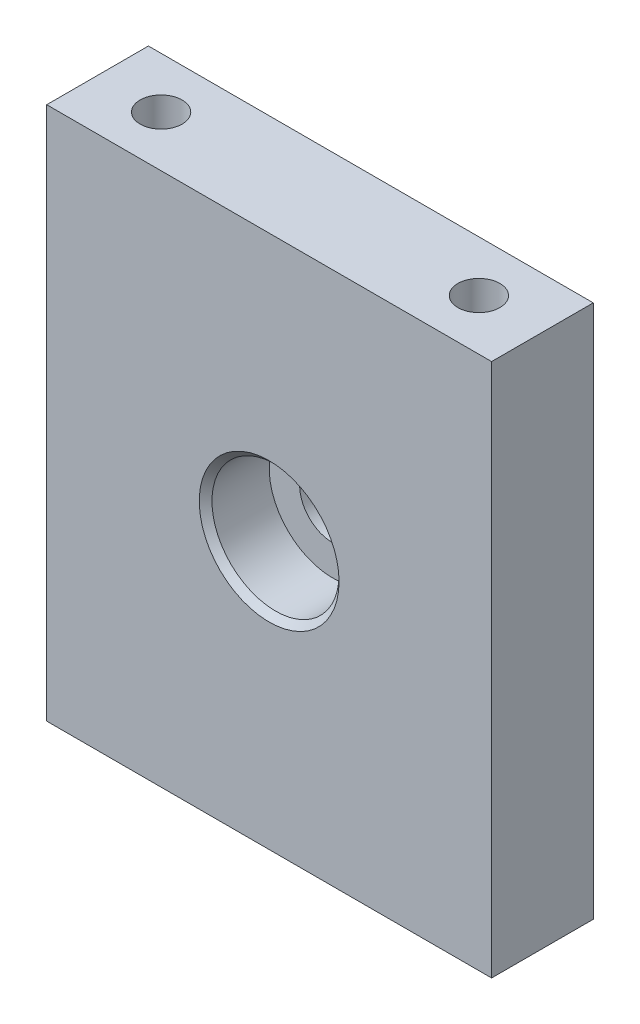
SolidWorks part; units mm, degrees
material "6061 合金"
ref_plane "前视基准面" through (0, 0, 0) normal (0, 0, 1) x (1, 0, 0)
ref_plane "上视基准面" through (0, 0, 0) normal (0, 1, 0) x (1, 0, 0)
ref_plane "右视基准面" through (0, 0, 0) normal (1, 0, 0) x (0, 0, -1)
sketch "草图1" plane through (0, 0, 0) normal (0, 0, 1) x (1, 0, 0)
  line L1 (-17.5, 21) -> (17.5, 21)
  line L2 (-17.5, 21) -> (-17.5, -21)
  line L3 (-17.5, -21) -> (17.5, -21)
  line L4 (17.5, 21) -> (17.5, -21)
  line L5 (-17.5, 21) -> (17.5, -21) construction
  line L6 (-17.5, -21) -> (17.5, 21) construction
  point P0 (0, 0)
  dimension "D1" = 42
  dimension "D2" = 35
extrude "凸台-拉伸1" add sketch "草图1" along normal mid plane 8
sketch "草图3" plane through (0, 21, 0) normal (0, 1, 0) x (1, 0, 0)
  line L0 (-12.5, 0) -> (12.5, 0) construction
  point P3 (0, 0)
  dimension "D1" = 25
sketch "草图4" plane through (0, 0, -4) normal (0, 0, -1) x (-1, 0, 0)
  line L1 (-5, 6) -> (5, 6)
  line L2 (-6, 5) -> (-6, -5)
  line L3 (-5, -6) -> (5, -6)
  line L4 (6, 5) -> (6, -5)
  line L5 (-6, 6) -> (6, -6) construction
  line L6 (-6, -6) -> (6, 6) construction
  circle A0 centre (0, 0) radius 10
  arc A1 (5, 6) -> (6, 5) centre (5, 5) cw
  arc A2 (5, -6) -> (6, -5) centre (5, -5) ccw
  arc A3 (-6, -5) -> (-5, -6) centre (-5, -5) ccw
  arc A4 (-5, 6) -> (-6, 5) centre (-5, 5) ccw
  dimension "D2" = 1
  dimension "D3" = 20
  dimension "D1" = 12
extrude "凸台-拉伸2" add sketch "草图4" along normal blind 3.5
sketch "草图5" plane through (0, 0, -4) normal (0, 0, -1) x (-1, 0, 0)
  line L4 (6, -5) -> (6, 5)
  line L5 (5, 6) -> (-5, 6)
  line L6 (-6, 5) -> (-6, -5)
  line L7 (-5, -6) -> (5, -6)
  line L8 (6, -5) -> (6, 5)
  line L9 (5, 6) -> (-5, 6)
  line L10 (-6, 5) -> (-6, -5)
  line L11 (-5, -6) -> (5, -6)
  arc A4 (6, 5) -> (5, 6) centre (5, 5) ccw
  arc A5 (-5, 6) -> (-6, 5) centre (-5, 5) ccw
  arc A6 (-6, -5) -> (-5, -6) centre (-5, -5) ccw
  arc A7 (5, -6) -> (6, -5) centre (5, -5) ccw
  arc A8 (6, 5) -> (5, 6) centre (5, 5) ccw
  arc A9 (-5, 6) -> (-6, 5) centre (-5, 5) ccw
  arc A10 (-6, -5) -> (-5, -6) centre (-5, -5) ccw
  arc A11 (5, -6) -> (6, -5) centre (5, -5) ccw
  dimension "D1" = 0
extrude "切除-拉伸2" cut sketch "草图5" against normal blind 2
sketch "草图6" plane through (0, 0, 4) normal (0, 0, 1) x (1, 0, 0)
  circle A0 centre (0, 0) radius 2.6
  dimension "D1" = 5.2
extrude "切除-拉伸3" cut sketch "草图6" against normal through all
sketch "草图7" plane through (0, 0, 4) normal (0, 0, 1) x (1, 0, 0)
  circle A0 centre (0, 0) radius 5
  dimension "D1" = 10
extrude "切除-拉伸4" cut sketch "草图7" against normal blind 5
chamfer "倒角1" distance 0.5 angle 45 8 edges at (0, 6, -7.5) (5.7071, 5.7071, -7.5) (-5.7071, 5.7071, -7.5) (6, 0, -7.5) (-6, 0, -7.5) (5.7071, -5.7071, -7.5) (-5.7071, -5.7071, -7.5) (0, -6, -7.5)
chamfer "倒角2" distance 0.5 angle 45 1 edges at (5, 0, 4)
chamfer "倒角3" distance 1 angle 45 1 edges at (10, 0, -4)
hole_wizard "M4 螺纹孔1" positions "草图8" profile "草图9" tap size "M4" standard "ISO" end condition through all
sketch "草图8" plane through (0, 21, 0) normal (0, 1, 0) x (1, 0, 0)
  point P0 (-12.5, 0)
  point P3 (12.5, 0)
sketch "草图9" plane through (-12.5, 21, 0) normal (1, 0, 0) x (0, 0, 1)
  line L0 (0, 0) -> (0, 42)
  line L1 (0, 42) -> (1.65, 42)
  line L2 (1.65, 42) -> (1.65, 0)
  line L5 (1.65, 0) -> (0, 0)
  line L11 (0, -6.35) -> (0, 107.95) construction
  dimension "通孔螺纹孔钻头直径" = 3.3
  dimension "通孔螺纹孔钻头深度" = 42
cosmetic thread "孔螺蚊线1" parameters "D2"=4
cosmetic thread "孔螺蚊线2" parameters "D2"=4
